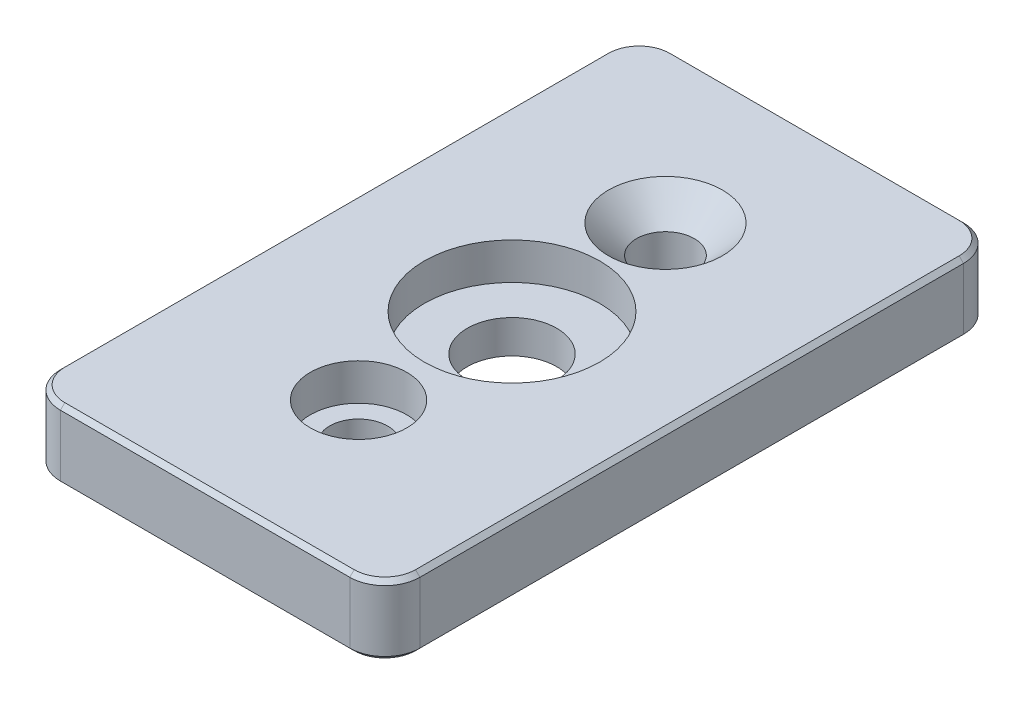
SolidWorks part; units mm, degrees
ref_plane "Front Plane" through (0, 0, 0) normal (0, 0, 1) x (1, 0, 0)
ref_plane "Top Plane" through (0, 0, 0) normal (0, 1, 0) x (1, 0, 0)
ref_plane "Right Plane" through (0, 0, 0) normal (1, 0, 0) x (0, 0, -1)
sketch "Sketch1" plane through (0, 0, 0) normal (0, 1, 0) x (1, 0, 0)
  line L1 (-20.5, -35) -> (20.5, -35)
  line L2 (-20.5, -35) -> (-20.5, 35)
  line L3 (-20.5, 35) -> (20.5, 35)
  line L4 (20.5, -35) -> (20.5, 35)
  line L5 (-20.5, -35) -> (20.5, 35) construction
  line L6 (-20.5, 35) -> (20.5, -35) construction
  circle A0 centre (0, 17.5) radius 3.3
  circle A1 centre (0, -17.5) radius 3.3
  point P0 (0, 0)
  dimension "D3" = 6.6
  dimension "D4" = 6.6
  dimension "D1" = 41
  dimension "D2" = 70
  dimension "D5" = 17.5
  dimension "D6" = 17.5
extrude "Boss-Extrude1" add sketch "Sketch1" along normal blind 8
sketch "Sketch2" plane through (0, 8, 0) normal (0, 1, 0) x (1, 0, 0)
  circle A0 centre (0, -17.5) radius 5.5
extrude "Cut-Extrude1" cut sketch "Sketch2" against normal blind 4.2
chamfer "Chamfer2" distance 3.2 angle 45 1 edges at (0, 8, -14.2)
fillet "Fillet1" radius 4 4 edges at (-20.5, 4, 35) (20.5, 4, 35) (20.5, 4, -35) (-20.5, 4, -35)
chamfer "Chamfer4" distance 0.5 angle 45 16 edges at (-20.5, 0, 0) (-19.3284, 0, 33.8284) (0, 0, 35) (19.3284, 0, 33.8284) (20.5, 0, 0) (-19.3284, 0, -33.8284) (19.3284, 0, -33.8284) (0, 0, -35) (-20.5, 8, 0) (-19.3284, 8, 33.8284) (0, 8, 35) (19.3284, 8, 33.8284) (20.5, 8, 0) (19.3284, 8, -33.8284) (0, 8, -35) (-19.3284, 8, -33.8284)
sketch "Sketch4" plane through (0, 8, 0) normal (0, 1, 0) x (1, 0, 0)
  line L0 (-16.5, 35) -> (16.5, 35) construction
  circle A0 centre (0, 0) radius 5.1
  dimension "D1" = 35
extrude "Cut-Extrude3" cut sketch "Sketch4" against normal through all
sketch "Sketch5" plane through (0, 8, 0) normal (0, 1, 0) x (1, 0, 0)
  circle A0 centre (0, 0) radius 10
extrude "Cut-Extrude4" cut sketch "Sketch5" against normal blind 4.2
